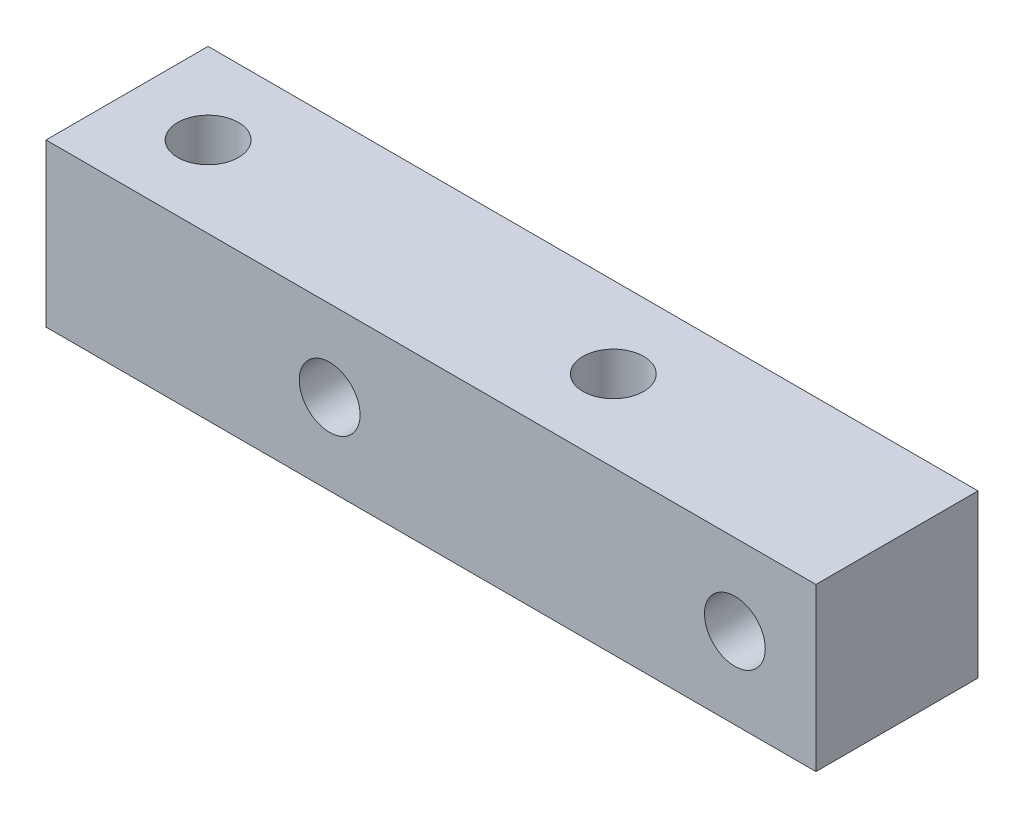
SolidWorks part; units mm, degrees
material "6061-T6 (SS)"
ref_plane "前视基准面" through (0, 0, 0) normal (0, 0, 1) x (1, 0, 0)
ref_plane "上视基准面" through (0, 0, 0) normal (0, 1, 0) x (1, 0, 0)
ref_plane "右视基准面" through (0, 0, 0) normal (1, 0, 0) x (0, 0, -1)
sketch "草图1" plane through (0, 0, 0) normal (0, 1, 0) x (1, 0, 0)
  line L0 (-19, 0) -> (19, 0) construction
  line L1 (-19, -4) -> (19, -4)
  line L2 (-19, -4) -> (-19, 4)
  line L3 (-19, 4) -> (19, 4)
  line L4 (19, -4) -> (19, 4)
  line L5 (-19, -4) -> (19, 4) construction
  line L6 (-19, 4) -> (19, -4) construction
  circle A0 centre (-15, 0) radius 1.5
  circle A1 centre (5, 0) radius 1.5
  point P0 (0, 0)
  dimension "D4" = 3
  dimension "D1" = 38
  dimension "D2" = 8
  dimension "D5" = 4
  dimension "D6" = 20
  dimension "D7" = 14
extrude "凸台-拉伸1" add sketch "草图1" along normal blind 8
cosmetic thread "装饰螺纹线3" parameters "D2"=4
cosmetic thread "装饰螺纹线4" parameters "D2"=4
sketch "草图2" plane through (0, 0, 4) normal (0, 0, 1) x (1, 0, 0)
  line L0 (-19, 8) -> (-19, 0) construction
  line L1 (-19, 8) -> (19, 8) construction
  circle A0 centre (-5, 4) radius 1.5
  circle A1 centre (15, 4) radius 1.5
  dimension "D2" = 3
  dimension "D3" = 4
  dimension "D6" = 4
  dimension "D1" = 14
  dimension "D4" = 20
extrude "切除-拉伸1" cut sketch "草图2" against normal through all
cosmetic thread "装饰螺纹线1"
cosmetic thread "装饰螺纹线2"
